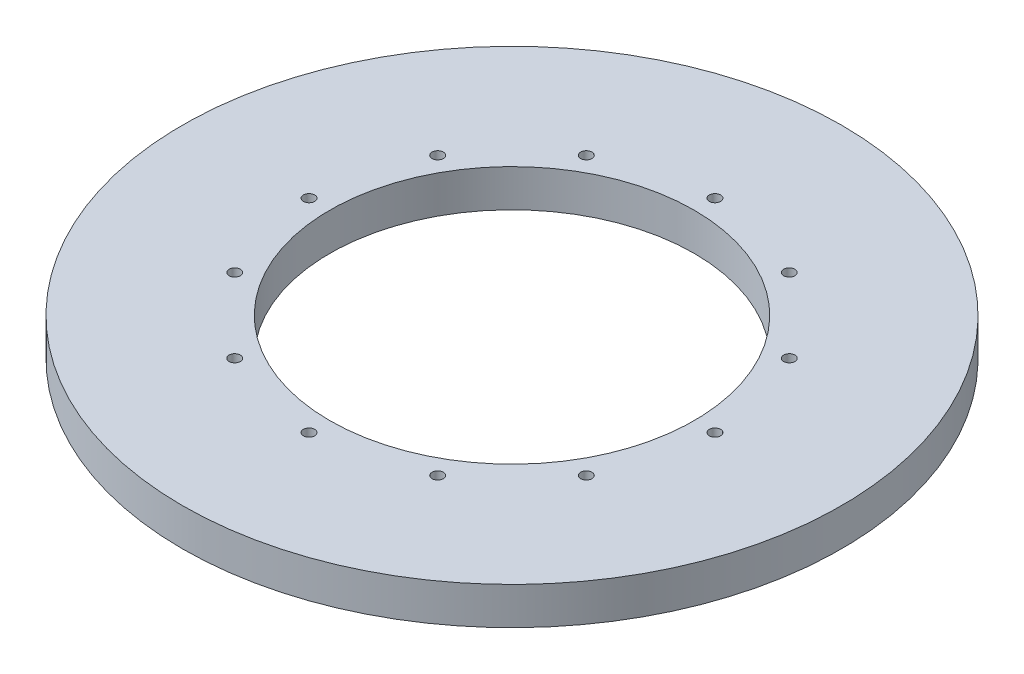
SolidWorks part; units mm, degrees
material "6061-T6 (SS)"
ref_plane "Front Plane" through (0, 0, 0) normal (0, 0, 1) x (1, 0, 0)
ref_plane "Top Plane" through (0, 0, 0) normal (0, 1, 0) x (1, 0, 0)
ref_plane "Right Plane" through (0, 0, 0) normal (1, 0, 0) x (0, 0, -1)
sketch "Sketch1" plane through (0, 0, 0) normal (0, 1, 0) x (1, 0, 0)
  line L5 (0, 0) -> (127.635, 0)
  line L6 (0, 0) -> (0, 127.635)
  line L7 (0, 127.635) -> (127.635, 127.635)
  line L8 (127.635, 0) -> (127.635, 127.635)
  dimension "D1" = 127.635
  dimension "D2" = 127.635
extrude "Boss-Extrude1" add sketch "Sketch1" along normal blind 9.525 contours L5 L8 L7 L6
sketch "Sketch12" plane through (0, 0, 0) normal (0, -1, 0) x (1, 0, 0)
  line L0 (63.8175, 0) -> (63.8175, -127.635) construction
  line L1 (0, 0) -> (127.635, 0) construction
  line L2 (0, -127.635) -> (127.635, -127.635) construction
  line L3 (0, -63.8175) -> (127.635, -63.8175) construction
  line L4 (0, 0) -> (0, -127.635) construction
  line L5 (127.635, 0) -> (127.635, -127.635) construction
  circle A0 centre (63.8175, -63.8175) radius 83.82
  dimension "D1" = 167.64
extrude "Boss-Extrude2" add sketch "Sketch12" against normal up to surface (9.525 mm away) contours A0 up to face at (63.8175, 9.525, -63.8175)
sketch "Sketch13" plane through (0, 0, 0) normal (0, -1, 0) x (-1, 0, 0)
  circle A0 centre (-63.8175, 63.8175) radius 83.82
  circle A1 centre (-63.8175, 63.8175) radius 104.9285
  dimension "D1" = 167.64
extrude "Cut-Extrude4" cut sketch "Sketch13" against normal up to surface (9.525 mm away) contours A1 | A0 up to face at (63.8175, 9.525, -63.8175)
sketch "Sketch5" plane through (0, 9.525, 0) normal (0, 1, 0) x (1, 0, 0)
  circle A0 centre (63.8175, 63.8175) radius 46.355
  circle A1 centre (63.8175, 63.8175) radius 83.82 construction
  dimension "D1" = 92.71
extrude "Cut-Extrude1" cut sketch "Sketch5" against normal blind 9.525
sketch "Sketch11" plane through (0, 9.525, 0) normal (0, 1, 0) x (1, 0, 0)
  line L0 (63.8175, 63.8175) -> (63.8175, 115.443) construction
  circle A0 centre (63.8175, 115.443) radius 1.4351
  dimension "D2" = 2.8702
  dimension "D1" = 51.6255
extrude "Cut-Extrude3" cut sketch "Sketch11" against normal through all contours A0
pattern_circular "CirPattern1" count 12 over 360 about axis through (63.8175, 0, -63.8175) along (0, 1, 0) of "Cut-Extrude3"
